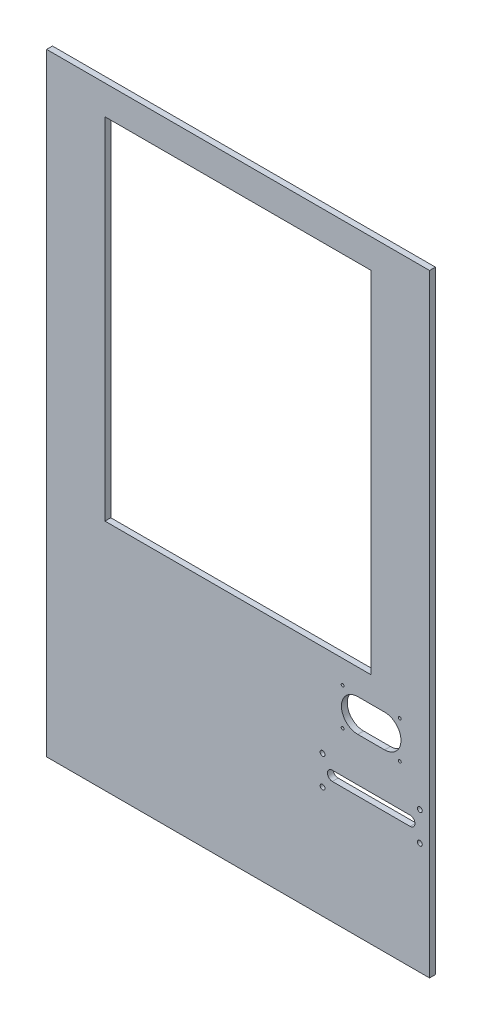
SolidWorks part; units mm, degrees
ref_plane "Front Plane" through (0, 0, 0) normal (0, 0, 1) x (1, 0, 0)
ref_plane "Top Plane" through (0, 0, 0) normal (0, 1, 0) x (1, 0, 0)
ref_plane "Right Plane" through (0, 0, 0) normal (1, 0, 0) x (0, 0, -1)
sketch "Sketch1" plane through (0, 0, 0) normal (0, 0, 1) x (1, 0, 0)
  line L0 (173.8, -128.728) -> (173.8, -171.4) construction
  line L1 (-250, 400) -> (250, 400)
  line L2 (-250, 400) -> (-250, -400)
  line L3 (-250, -400) -> (250, -400)
  line L4 (250, 400) -> (250, -400)
  line L5 (-250, 400) -> (250, -400) construction
  line L6 (-250, -400) -> (250, 400) construction
  line L7 (-173.8, 361.9) -> (173.8, 361.9)
  line L8 (-173.8, 361.9) -> (-173.8, -95.3)
  line L9 (-173.8, -95.3) -> (173.8, -95.3)
  line L10 (173.8, 361.9) -> (173.8, -95.3)
  line L11 (-173.8, 361.9) -> (173.8, -95.3) construction
  line L12 (-173.8, -95.3) -> (173.8, 361.9) construction
  line L13 (156.274, -128.728) -> (191.326, -128.728)
  line L15 (156.274, -171.4) -> (191.326, -171.4)
  line L17 (156.274, -128.728) -> (191.326, -171.4) construction
  line L18 (156.274, -171.4) -> (191.326, -128.728) construction
  line L19 (134.938, -150.064) -> (212.662, -150.064) construction
  line L20 (224.6, -234.9) -> (123, -234.9) construction
  line L21 (224.6, -241.25) -> (123, -241.25)
  line L22 (224.6, -228.55) -> (123, -228.55)
  line L23 (230.95, -234.9) -> (250, -234.9) construction
  line L24 (173.8, -233.9333) -> (173.8, -259.3333) construction
  arc A0 (156.274, -128.728) -> (156.274, -171.4) centre (156.274, -150.064) ccw
  arc A1 (191.326, -128.728) -> (191.326, -171.4) centre (191.326, -150.064) cw
  circle A2 centre (136.462, -125.68) radius 1.905
  circle A3 centre (211.138, -125.68) radius 1.905
  circle A4 centre (211.138, -174.448) radius 1.905
  circle A5 centre (136.462, -174.448) radius 1.905
  arc A6 (224.6, -241.25) -> (224.6, -228.55) centre (224.6, -234.9) ccw
  arc A7 (123, -228.55) -> (123, -241.25) centre (123, -234.9) ccw
  circle A8 centre (237.3, -215.85) radius 3.175
  circle A9 centre (110.3, -215.85) radius 3.175
  circle A10 centre (237.3, -253.95) radius 3.175
  circle A11 centre (110.3, -253.95) radius 3.175
  point P0 (0, 0)
  point P6 (0, 133.3)
  point P11 (173.8, -150.064)
  point P32 (173.8, -234.9)
  point P43 (0, 0)
  point P44 (0, 0)
  point P45 (0, 0)
  dimension "D9" = 76.2
  dimension "D11" = 3.81
  dimension "D18" = 12.7
  dimension "D19" = 184.15
  dimension "D20" = 6.35
  dimension "D1" = 500
  dimension "D2" = 800
  dimension "D3" = 38.1
  dimension "D4" = 76.2
  dimension "D5" = 76.2
  dimension "D6" = 457.2
  dimension "D7" = 42.672
  dimension "D8" = 35.052
  dimension "D10" = 228.6
  dimension "D12" = 37.338
  dimension "D13" = 3.048
  dimension "D14" = 12.7
  dimension "D15" = 25.4
  dimension "D16" = 101.6
  dimension "D17" = 165.1
  dimension "D21" = 76.2
  dimension "D22" = 25.4
extrude "Boss-Extrude1" add sketch "Sketch1" along normal blind 7.62
